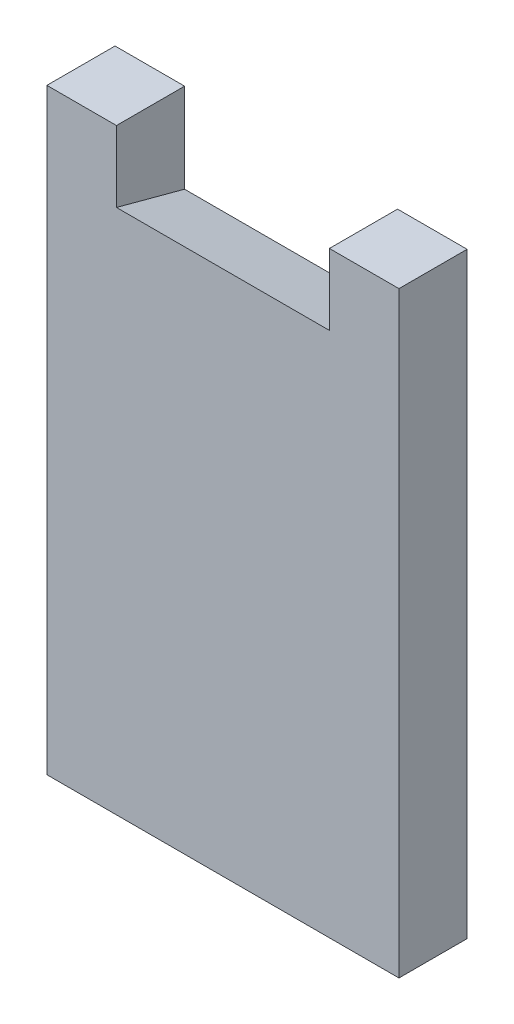
SolidWorks part; units mm, degrees
ref_plane "前视基准面" through (0, 0, 0) normal (0, 0, 1) x (1, 0, 0)
ref_plane "上视基准面" through (0, 0, 0) normal (0, 1, 0) x (1, 0, 0)
ref_plane "右视基准面" through (0, 0, 0) normal (1, 0, 0) x (0, 0, -1)
sketch "草图1" plane through (0, 0, 0) normal (0, 0, 1) x (1, 0, 0)
  line L1 (0, 0) -> (49.6, 0)
  line L2 (0, 0) -> (0, -84.11)
  line L3 (0, -84.11) -> (49.6, -84.11)
  line L4 (49.6, 0) -> (49.6, -84.11)
  line L5 (9.8, 0) -> (39.8, 0)
  line L6 (9.8, 0) -> (9.8, -10)
  line L7 (9.8, -10) -> (39.8, -10)
  line L8 (39.8, 0) -> (39.8, -10)
  point P9 (24.8, 0)
  dimension "D1" = 10
  dimension "D2" = 49.6
  dimension "D3" = 30
  dimension "D4" = 74.11
extrude "凸台-拉伸1" add sketch "草图1" along normal blind 9.6 contours L1 L8 L7 L6 L2 L3 L4
draft "拔模5" type of draft neutral plane draft angle 15 faces to draft 1 face at (24.8, -10, 4.8) neutral plane through (0, 0, 9.6) neutral plane normal (0, 0, 1) reverse direction yes parameters "D1"=15
